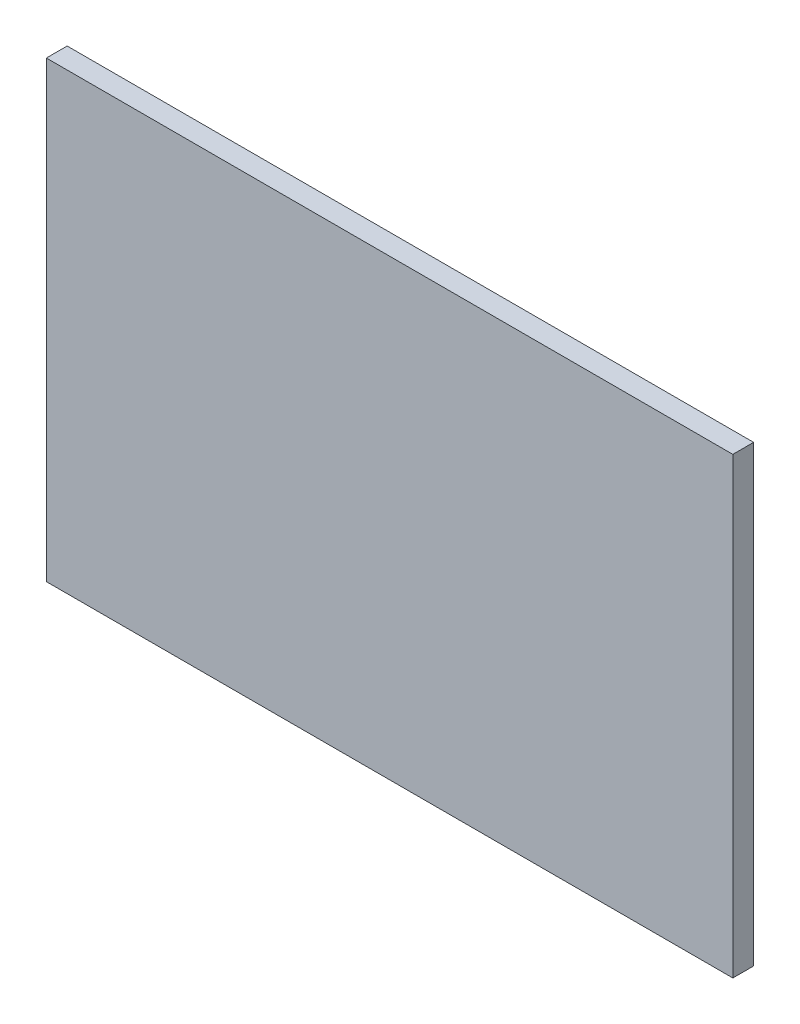
SolidWorks part; units mm, degrees
ref_plane "前视基准面" through (0, 0, 0) normal (0, 0, 1) x (1, 0, 0)
ref_plane "上视基准面" through (0, 0, 0) normal (0, 1, 0) x (1, 0, 0)
ref_plane "右视基准面" through (0, 0, 0) normal (1, 0, 0) x (0, 0, -1)
sketch "草图1" plane through (0, 0, 0) normal (0, 0, 1) x (1, 0, 0)
  line L1 (-82.5, 54.5) -> (82.5, 54.5)
  line L2 (-82.5, 54.5) -> (-82.5, -54.5)
  line L3 (-82.5, -54.5) -> (82.5, -54.5)
  line L4 (82.5, 54.5) -> (82.5, -54.5)
  line L5 (-82.5, 54.5) -> (82.5, -54.5) construction
  line L6 (-82.5, -54.5) -> (82.5, 54.5) construction
  point P0 (0, 0)
  dimension "D1" = 109
  dimension "D2" = 165
extrude "凸台-拉伸1" add sketch "草图1" along normal blind 5
